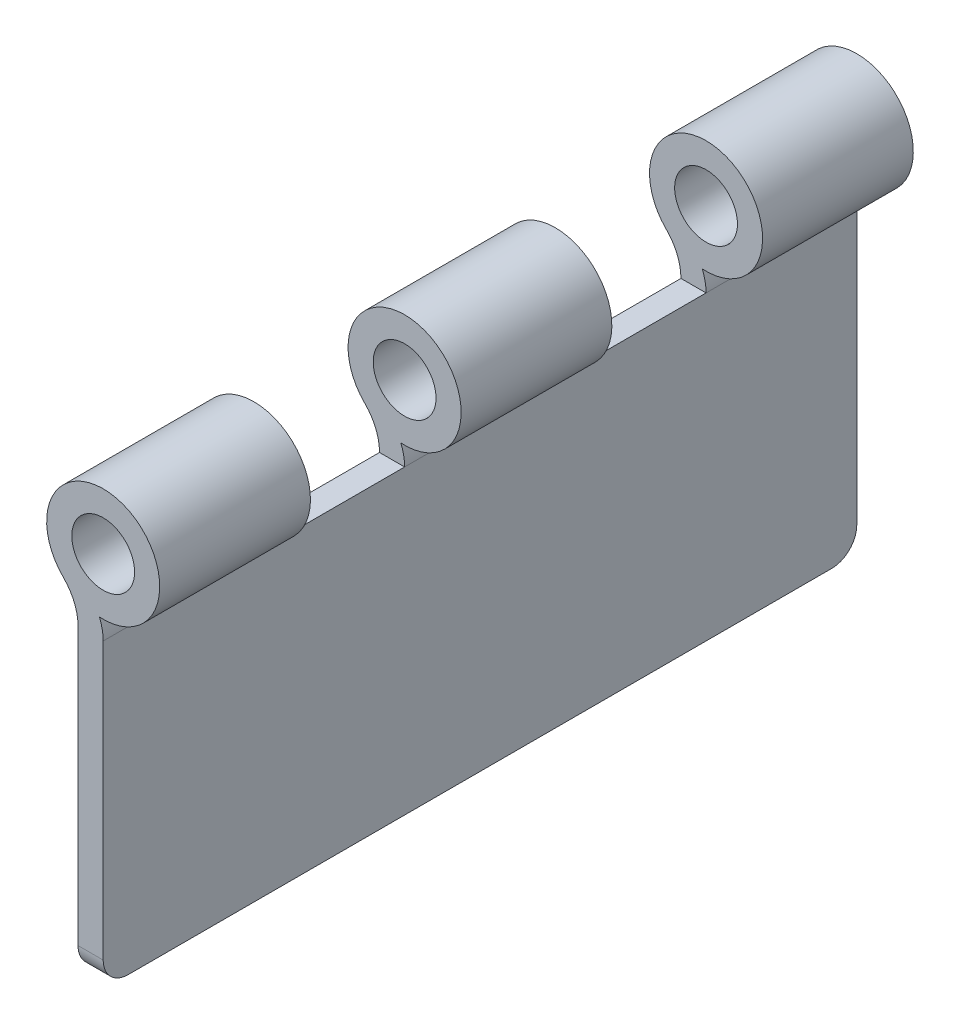
SolidWorks part; units mm, degrees
ref_plane "Front Plane" through (0, 0, 0) normal (0, 0, 1) x (1, 0, 0)
ref_plane "Top Plane" through (0, 0, 0) normal (0, 1, 0) x (1, 0, 0)
ref_plane "Right Plane" through (0, 0, 0) normal (1, 0, 0) x (0, 0, -1)
sketch "Sketch1" plane through (0, 0, 0) normal (0, 0, 1) x (1, 0, 0)
  line L0 (0, 0) -> (-2.54, 0)
  line L1 (-2.54, 0) -> (-2.54, 30.48)
  line L2 (0, 0) -> (0, 30.48)
  circle A0 centre (0, 38.1) radius 5.715
  arc A1 (-2.54, 30.48) -> (-4.0242, 34.042) centre (-7.5565, 30.48) ccw
  arc A2 (0, 30.48) -> (-0.381, 32.3977) centre (-5.0165, 30.48) ccw
  circle A3 centre (0, 38.1) radius 3.175
  dimension "D1" = 11.43
  dimension "D4" = 7.62
  dimension "D5" = 6.35
  dimension "D2" = 2.54
  dimension "D3" = 38.1
extrude "Boss-Extrude1" add sketch "Sketch1" along normal mid plane 76.2 contours L2 A2 A0 A1 L1 L0 | A0 A3
ref_plane "Plane1" through (0, 0, 15.24) normal (0, 0, 1) x (1, 0, 0)
sketch "Sketch2" plane through (0, 0, 15.24) normal (0, 0, 1) x (1, 0, 0)
  line L0 (0, 30.48) -> (-2.54, 30.48)
  arc A0 (0, 30.48) -> (-0.381, 32.3977) centre (-5.0165, 30.48) ccw construction
  arc A1 (-2.54, 30.48) -> (-4.0242, 34.042) centre (-7.5565, 30.48) ccw construction
  circle A2 centre (0, 38.1) radius 3.175 construction
  arc A3 (-0.381, 32.3977) -> (-4.0242, 34.042) centre (0, 38.1) ccw construction
  arc A4 (0, 30.48) -> (-0.381, 32.3977) centre (-5.0165, 30.48) ccw
  arc A5 (-2.54, 30.48) -> (-4.0242, 34.042) centre (-7.5565, 30.48) ccw
  circle A6 centre (0, 38.1) radius 3.175
  arc A7 (-0.381, 32.3977) -> (-4.0242, 34.042) centre (0, 38.1) ccw
extrude "Cut-Extrude1" cut sketch "Sketch2" against normal mid plane 15.24 contours A4 A7 A5 L0 A6
mirror "Mirror1" about plane through (0, 0, 0) normal (0, 0, 1) of "Cut-Extrude1"
fillet "Fillet1" radius 2.54 2 edges at (-1.27, 0, -38.1) (-1.27, 0, 38.1)
